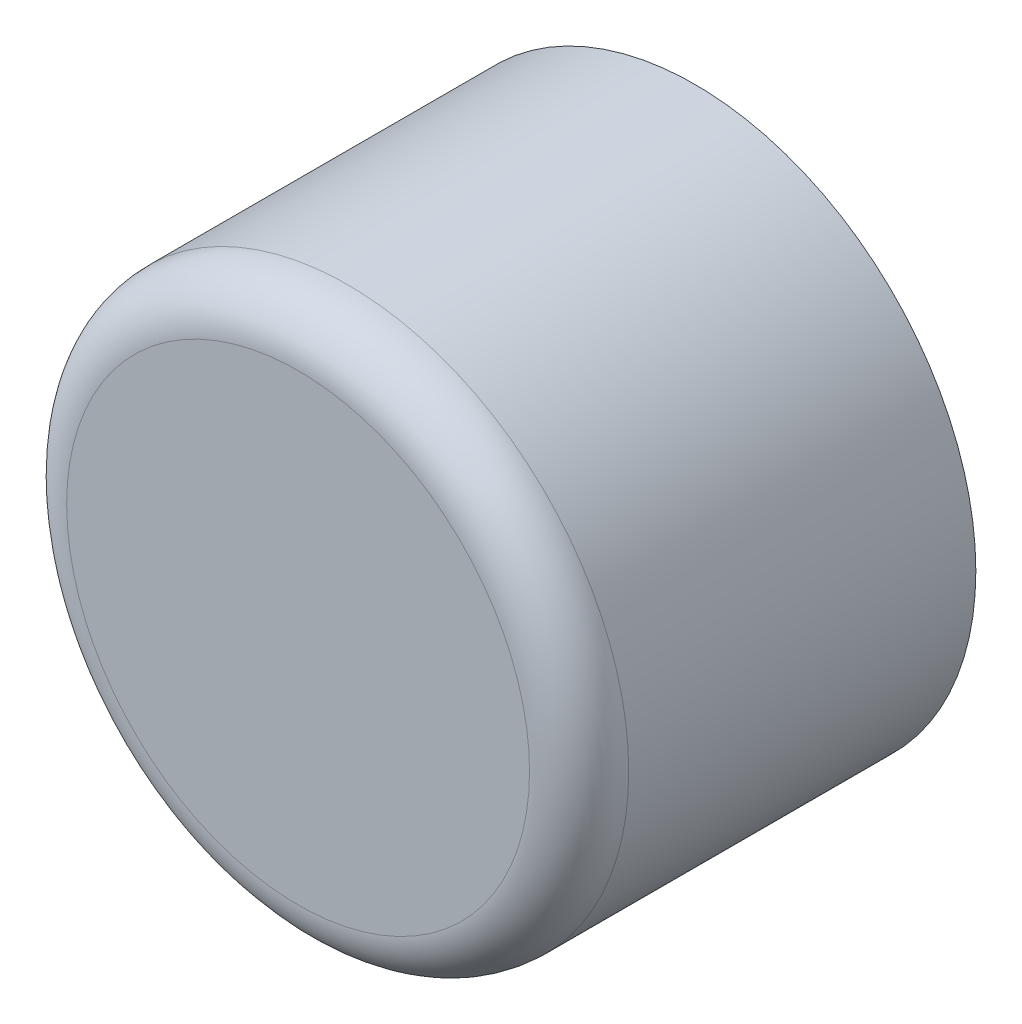
SolidWorks part; units mm, degrees
ref_plane "Спереди" through (0, 0, 0) normal (0, 0, 1) x (1, 0, 0)
ref_plane "Сверху" through (0, 0, 0) normal (0, 1, 0) x (1, 0, 0)
ref_plane "Справа" through (0, 0, 0) normal (1, 0, 0) x (0, 0, -1)
sketch "Эскиз1" plane through (0, 0, 0) normal (0, 0, 1) x (1, 0, 0)
  circle A0 centre (0, 0) radius 8.5
extrude "Бобышка-Вытянуть1" add sketch "Эскиз1" along normal blind 12
fillet "Скругление1" radius 1.5 1 edges at (8.5, 0, 12)
